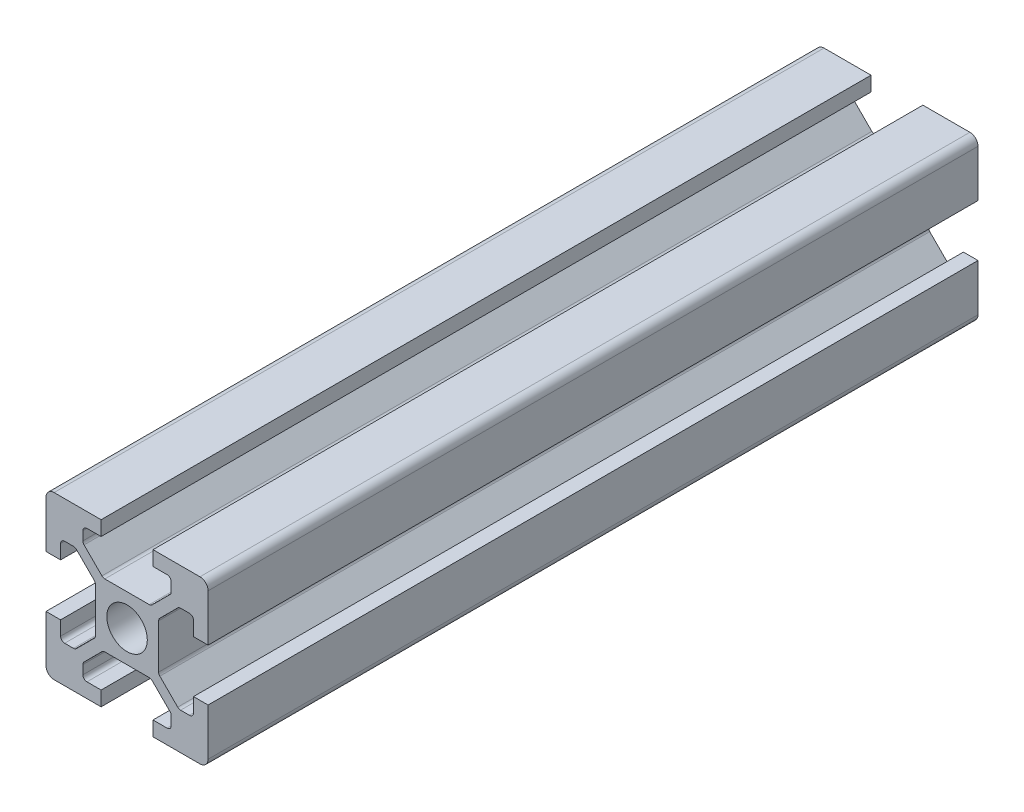
SolidWorks part; units mm, degrees
material "1060 Alloy"
ref_plane "Front Plane" through (0, 0, 0) normal (0, 0, 1) x (1, 0, 0)
ref_plane "Top Plane" through (0, 0, 0) normal (0, 1, 0) x (1, 0, 0)
ref_plane "Right Plane" through (0, 0, 0) normal (1, 0, 0) x (0, 0, -1)
sketch "Sketch1" plane through (0, 0, 0) normal (0, 0, 1) x (1, 0, 0)
  line L0 (20, 0) -> (-8.059, 28.059) construction
  line L1 (0, 0) -> (6.8, 0)
  line L2 (0, 0) -> (0, 6.8)
  line L3 (0, 20) -> (6.8, 20)
  line L4 (20, 0) -> (20, 6.8)
  line L5 (6.8, 20) -> (6.8, 18.2)
  line L6 (20, 20) -> (8.2322, 8.2322) construction
  line L7 (12.95, 6.1) -> (7.05, 6.1)
  line L8 (13.9, 7.05) -> (13.9, 12.95)
  line L9 (12.95, 13.9) -> (7.05, 13.9)
  line L10 (6.1, 7.05) -> (6.1, 12.95)
  line L11 (13.9, 6.1) -> (6.1, 13.9) construction
  line L12 (13.9, 13.9) -> (6.1, 6.1) construction
  line L13 (4.55, 16.4) -> (7.05, 13.9)
  line L14 (13.2, 18.2) -> (13.2, 20)
  line L15 (1.8, 6.8) -> (0, 6.8)
  line L16 (0, 13.2) -> (0, 20)
  line L17 (0, 13.2) -> (1.8, 13.2)
  line L18 (10, 10) -> (10, 13.9) construction
  line L19 (16.4, 4.55) -> (13.9, 7.05)
  line L20 (4.55, 16.4) -> (4.55, 18.2)
  line L21 (4.55, 18.2) -> (6.8, 18.2)
  line L22 (13.2, 18.2) -> (15.45, 18.2)
  line L23 (15.45, 18.2) -> (15.45, 16.4)
  line L24 (15.45, 16.4) -> (12.95, 13.9)
  line L25 (16.4, 4.55) -> (18.2, 4.55)
  line L26 (18.2, 4.55) -> (18.2, 6.8)
  line L27 (20, 6.8) -> (18.2, 6.8)
  line L28 (18.2, 13.2) -> (20, 13.2)
  line L29 (18.2, 13.2) -> (18.2, 15.45)
  line L30 (18.2, 15.45) -> (16.4, 15.45)
  line L31 (16.4, 15.45) -> (13.9, 12.95)
  line L32 (1.8, 4.55) -> (3.6, 4.55)
  line L33 (3.6, 15.45) -> (6.1, 12.95)
  line L34 (3.6, 15.45) -> (1.8, 15.45)
  line L35 (1.8, 15.45) -> (1.8, 13.2)
  line L36 (0, 13.2) -> (1.8, 13.2)
  line L37 (1.8, 6.8) -> (0, 6.8)
  line L38 (3.6, 4.55) -> (6.1, 7.05)
  line L39 (1.8, 6.8) -> (1.8, 4.55)
  line L40 (15.45, 3.6) -> (12.95, 6.1)
  line L41 (4.55, 3.6) -> (7.05, 6.1)
  line L42 (4.55, 1.8) -> (4.55, 3.6)
  line L43 (6.8, 1.8) -> (4.55, 1.8)
  line L44 (6.8, 1.8) -> (6.8, 0)
  line L45 (15.45, 3.6) -> (15.45, 1.8)
  line L46 (15.45, 1.8) -> (13.2, 1.8)
  line L47 (13.2, 0) -> (13.2, 1.8)
  line L48 (13.2, 20) -> (20, 20)
  line L49 (20, 13.2) -> (20, 20)
  line L50 (13.2, 0) -> (20, 0)
  line L51 (6.1, 6.1) -> (-5.5045, -5.5045) construction
  circle A0 centre (10, 10) radius 2.5
  point P25 (10, 16.4)
  point P39 (13.2, 19.1)
  point P46 (0.9, 6.8)
  dimension "D3" = 5
  dimension "D2" = 20
  dimension "D4" = 7.8
  dimension "D5" = 7.8
  dimension "D6" = 6.8
  dimension "D7" = 6.8
  dimension "D8" = 1.8
  dimension "D9" = 10.9
  dimension "D10" = 1.8
  dimension "D11" = 10.9
  dimension "D12" = 20
extrude "Boss-Extrude1" add sketch "Sketch1" along normal blind 95 contours L47 L50 L4 L27 L26 L25 L19 L8 L31 L30 L29 L28 L49 L48 L14 L22 L23 L24 L9 L13 L20 L21 L5 L3 L16 L17 L35 L34 L33 L10 L38 L32 L39 L15 L2 L1 L44 L43 L42 L41 L7 L40 L45 L46 A0
fillet "Fillet1" radius 1 4 edges at (20, 20, 47.5) (20, 0, 47.5) (0, 0, 47.5) (0, 20, 47.5)
fillet "Fillet2" radius 0.5 6 edges at (4.55, 18.2, 47.5) (4.55, 16.4, 47.5) (7.05, 13.9, 47.5) (15.45, 18.2, 47.5) (15.45, 16.4, 47.5) (12.95, 13.9, 47.5)
fillet "Fillet3" radius 0.5 6 edges at (18.2, 15.45, 47.5) (16.4, 15.45, 47.5) (13.9, 12.95, 47.5) (18.2, 4.55, 47.5) (13.9, 7.05, 47.5) (16.4, 4.55, 47.5)
fillet "Fillet4" radius 0.5 6 edges at (1.8, 15.45, 47.5) (3.6, 15.45, 47.5) (6.1, 12.95, 47.5) (3.6, 4.55, 47.5) (1.8, 4.55, 47.5) (6.1, 7.05, 47.5)
fillet "Fillet5" radius 0.5 6 edges at (7.05, 6.1, 47.5) (4.55, 3.6, 47.5) (4.55, 1.8, 47.5) (15.45, 1.8, 47.5) (15.45, 3.6, 47.5) (12.95, 6.1, 47.5)
